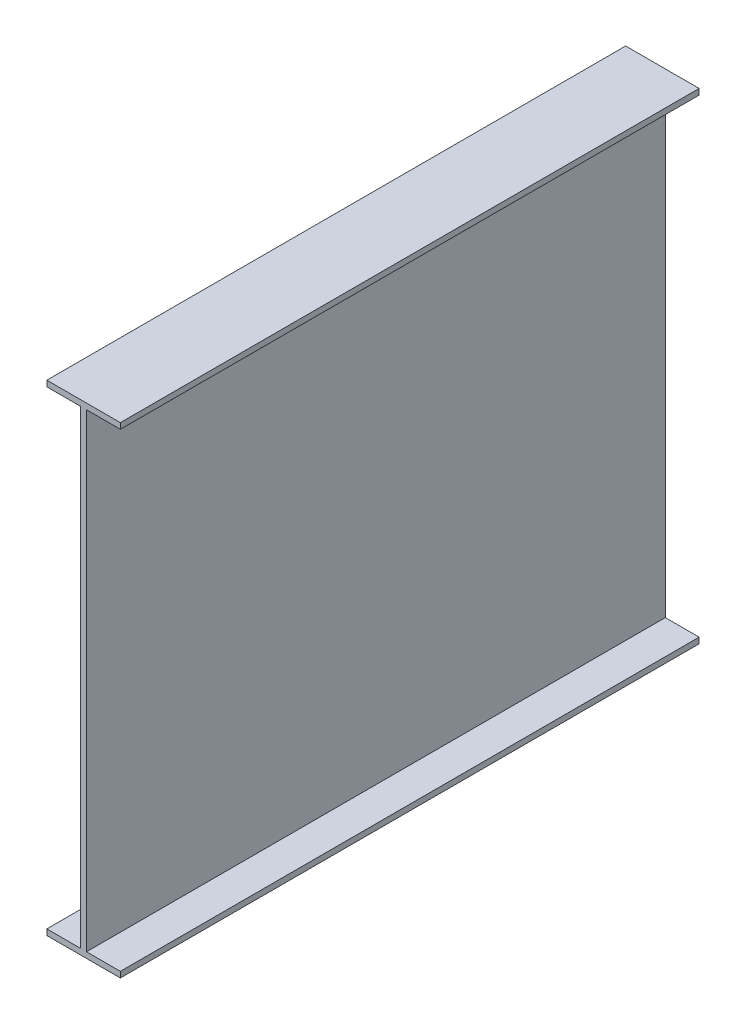
SolidWorks part; units mm, degrees
ref_plane "Front Plane" through (0, 0, 0) normal (0, 0, 1) x (1, 0, 0)
ref_plane "Top Plane" through (0, 0, 0) normal (0, 1, 0) x (1, 0, 0)
ref_plane "Right Plane" through (0, 0, 0) normal (1, 0, 0) x (0, 0, -1)
sketch "Sketch1" plane through (0, 0, 0) normal (0, 0, 1) x (1, 0, 0)
  line L2 (0, 0) -> (0, 811)
  line L4 (10, 0) -> (10, 811)
  line L6 (-58.5, 811) -> (-58.5, 821)
  line L7 (-58.5, 821) -> (68.5, 821)
  line L8 (68.5, 811) -> (68.5, 821)
  line L10 (-58.5, 811) -> (0, 811)
  line L11 (-58.5, -10) -> (-58.5, 0)
  line L12 (-58.5, 0) -> (0, 0)
  line L13 (-58.5, -10) -> (68.5, -10)
  line L14 (68.5, -10) -> (68.5, 0)
  line L15 (10, 0) -> (68.5, 0)
  line L16 (10, 811) -> (68.5, 811)
  dimension "D1" = 10
  dimension "D2" = 811
  dimension "D3" = 10
  dimension "D4" = 127
  dimension "D5" = 58.5
  dimension "D6" = 127
  dimension "D7" = 58.5
extrude "Boss-Extrude1" add sketch "Sketch1" against normal blind 1000
